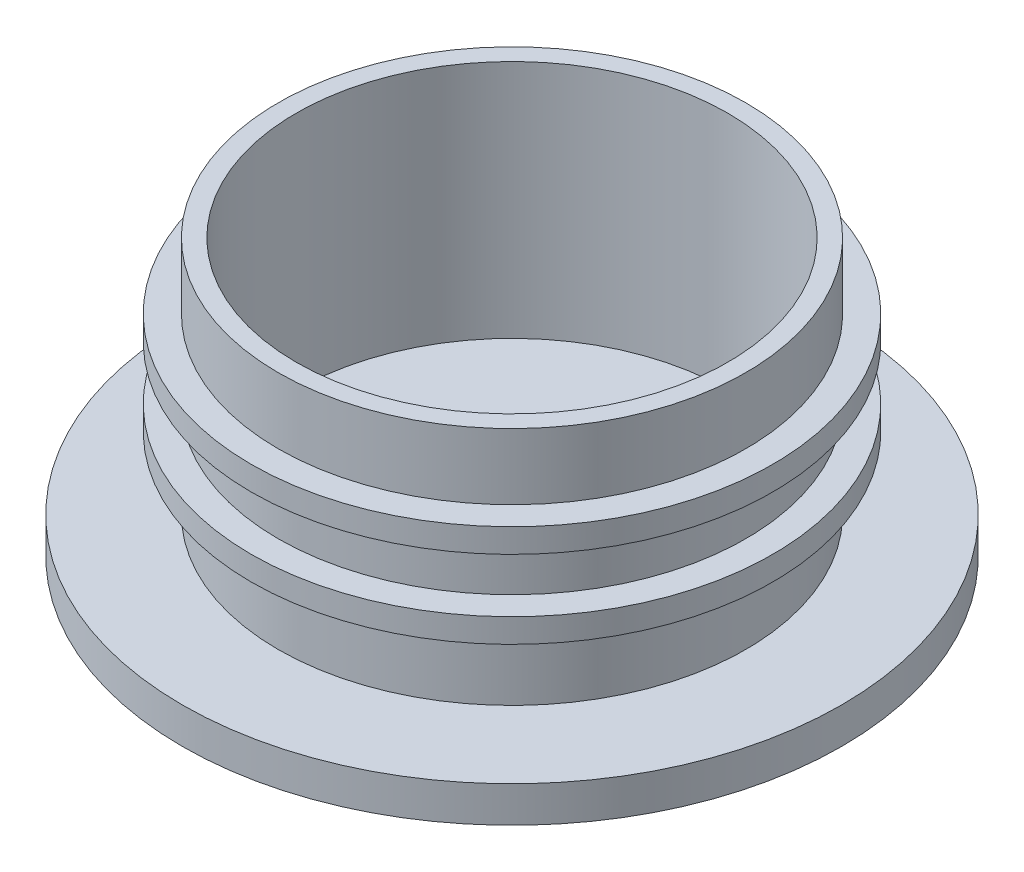
SolidWorks part; units mm, degrees
ref_plane "前基準面" through (0, 0, 0) normal (0, 0, 1) x (1, 0, 0)
ref_plane "上基準面" through (0, 0, 0) normal (0, 1, 0) x (1, 0, 0)
ref_plane "右基準面" through (0, 0, 0) normal (1, 0, 0) x (0, 0, -1)
sketch "草圖1" plane through (0, 0, 0) normal (0, 1, 0) x (1, 0, 0)
  circle A0 centre (0, 0) radius 19.5
  circle A1 centre (0, 0) radius 18
  dimension "D1" = 39
  dimension "D2" = 36
extrude "填料-伸長1" add sketch "草圖1" along normal blind 20
sketch "草圖3" plane through (0, 0, 0) normal (0, -1, 0) x (1, 0, 0)
  circle A0 centre (0, 0) radius 27.5
  dimension "D1" = 55
extrude "填料-伸長2" add sketch "草圖3" along normal blind 3
ref_plane "平面1" through (0, 8, 0) normal (0, 1, 0) x (1, 0, 0)
sketch "草圖4" plane through (0, 8, 0) normal (0, 1, 0) x (1, 0, 0)
  circle A0 centre (0, 0) radius 21.75
  dimension "D1" = 43.5
extrude "填料-伸長3" add sketch "草圖4" against normal blind 2
sketch "草圖6" plane through (0, 0, 0) normal (0, 1, 0) x (1, 0, 0)
  circle A0 centre (0, 0) radius 18
  dimension "D1" = 36
ref_plane "平面2" through (0, 11.5, 0) normal (0, 1, 0) x (1, 0, 0)
sketch "草圖8" plane through (0, 11.5, 0) normal (0, 1, 0) x (1, 0, 0)
  circle A0 centre (0, 0) radius 21.75
extrude "填料-伸長4" add sketch "草圖8" along normal blind 2 from offset 1
extrude "除料-伸長1" cut sketch "草圖6" along normal blind 35
ref_plane "平面3" through (0, -3, 0) normal (0, -1, 0) x (-1, 0, 0)
sketch "草圖10" plane through (0, -3, 0) normal (0, -1, 0) x (-1, 0, 0)
  circle A0 centre (0, 0) radius 25
  dimension "D1" = 50
ref_plane "平面4" through (0, -33, 0) normal (0, -1, 0) x (-1, 0, 0)
sketch "草圖11" plane through (0, -33, 0) normal (0, -1, 0) x (-1, 0, 0)
  circle A0 centre (0, 0) radius 5
  dimension "D1" = 10
sketch "草圖13" plane through (0, 0, 0) normal (1, 0, 0) x (0, 0, -1)
  line L0 (0, -3) -> (0, -45.3687) construction
  line L2 (-25, -3) -> (25, -3) construction
  line L4 (-5, -33) -> (5, -33) construction
  arc A0 (-25, -3) -> (-5, -33) centre (41.6009, 19.734) ccw
  arc A1 (25, -3) -> (5, -33) centre (-41.6009, 19.734) cw
sketch "草圖16" plane through (0, 0, 0) normal (1, 0, 0) x (0, 0, -1)
  line L6 (0, 20) -> (0, -45.718) construction
  line L7 (18, 20) -> (-18, 20) construction
  line L12 (-4.9585, -34.1658) -> (-13.1333, -28.1434)
  line L13 (-13.1333, -28.1434) -> (-20.094, -19.8043)
  line L14 (-20.094, -19.8043) -> (-25.0562, -8.7774)
  line L15 (-25.0562, -8.7774) -> (-26.3656, -3)
  line L16 (-30.25, -3) -> (30.25, -3) construction
  line L18 (4.9585, -34.1658) -> (13.1333, -28.1434)
  line L19 (13.1333, -28.1434) -> (20.094, -19.8043)
  line L20 (20.094, -19.8043) -> (25.0562, -8.7774)
  line L21 (25.0562, -8.7774) -> (26.3656, -3)
  line L22 (-26.3656, -3) -> (26.3656, -3)
  line L23 (4.9585, -34.1658) -> (0, -37.132)
  line L24 (-4.9585, -34.1658) -> (0, -37.132)
